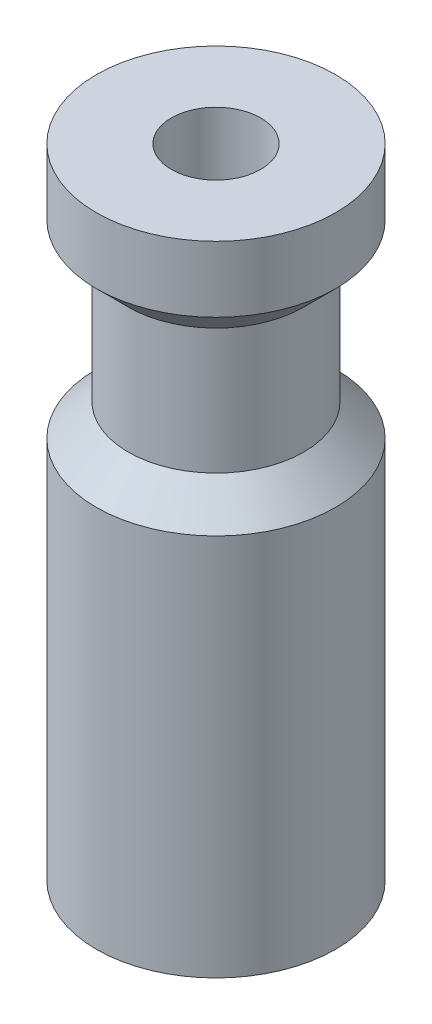
SolidWorks part; units mm, degrees
ref_plane "Front Plane" through (0, 0, 0) normal (0, 0, 1) x (1, 0, 0)
ref_plane "Top Plane" through (0, 0, 0) normal (0, 1, 0) x (1, 0, 0)
ref_plane "Right Plane" through (0, 0, 0) normal (1, 0, 0) x (0, 0, -1)
sketch "Sketch2" plane through (0, 0, 0) normal (0, 0, 1) x (1, 0, 0)
  line L0 (0, 12.7) -> (0, -12.7)
  line L1 (0, 12.7) -> (4.7625, 12.7)
  line L2 (4.7625, 12.7) -> (4.7625, 10.08)
  line L4 (3.4925, 8.81) -> (3.4925, 3.81)
  line L6 (4.7625, 2.54) -> (4.7625, -12.7)
  line L7 (4.7625, -12.7) -> (0, -12.7)
  line L8 (3.4925, 8.81) -> (4.7625, 10.08)
  line L9 (3.4925, 3.81) -> (4.7625, 2.54)
  point P3 (0, 0)
  dimension "D1" = 5
  dimension "D2" = 1.27
  dimension "D3" = 4.7625
  dimension "D4" = 4.7625
  dimension "D5" = 1.27
  dimension "D6" = 16.51
  dimension "D7" = 25.4
revolve "Revolve1" add sketch "Sketch2" angle 360 about L0
sketch "Sketch3" plane through (0, 12.7, 0) normal (0, 1, 0) x (1, 0, 0)
  circle A0 centre (0, 0) radius 1.778
  dimension "D1" = 3.556
extrude "Cut-Extrude1" cut sketch "Sketch3" against normal blind 27.94
